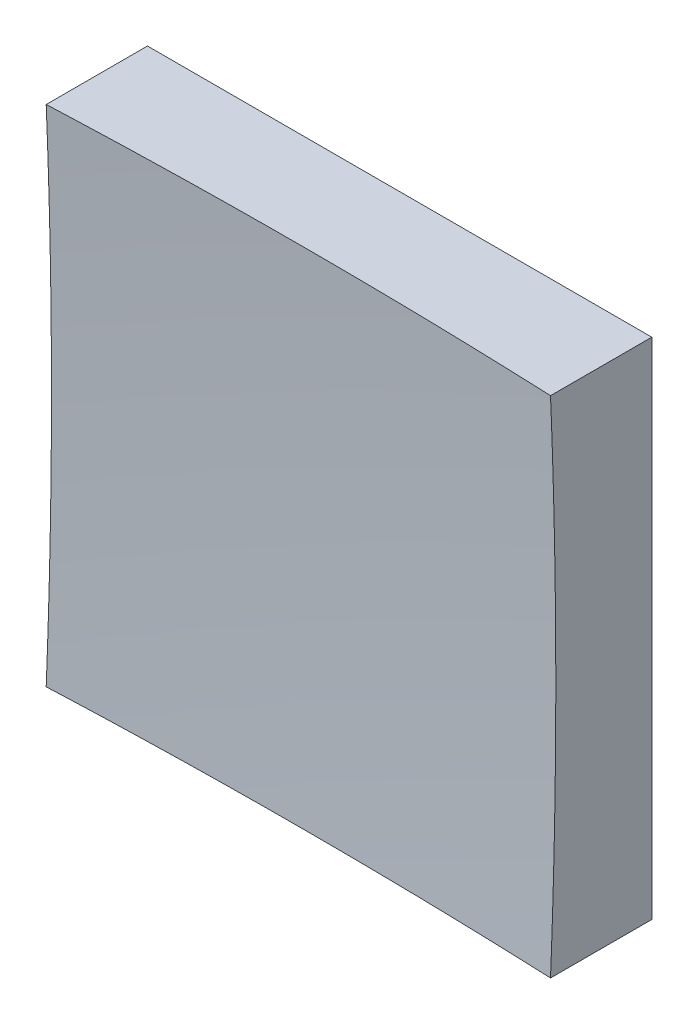
SolidWorks part; units mm, degrees
ref_plane "前视基准面" through (0, 0, 0) normal (0, 0, 1) x (1, 0, 0)
ref_plane "上视基准面" through (0, 0, 0) normal (0, 1, 0) x (1, 0, 0)
ref_plane "右视基准面" through (0, 0, 0) normal (1, 0, 0) x (0, 0, -1)
sketch "草图1" plane through (0, 0, 0) normal (0, 0, 1) x (1, 0, 0)
  line L1 (-25, 25) -> (25, 25)
  line L2 (-25, 25) -> (-25, -25)
  line L3 (-25, -25) -> (25, -25)
  line L4 (25, 25) -> (25, -25)
  line L5 (-25, 25) -> (25, -25) construction
  line L6 (-25, -25) -> (25, 25) construction
  point P0 (0, 0)
  dimension "D1" = 50
  dimension "D2" = 50
extrude "凸台-拉伸1" add sketch "草图1" along normal blind 50 contours L2 L3 L4 L1
sketch "草图2" plane through (0, 0, 0) normal (0, 1, 0) x (1, 0, 0)
  line L0 (-7.4603, -9) -> (7.3192, -9) construction
  line L1 (0, 0) -> (0, -12.1749) construction
  line L2 (584.9073, -475.2709) -> (0, -475.2709)
  line L3 (0, -475.2709) -> (0, -9)
  arc A1 (584.9073, -475.2709) -> (0, -9) centre (0, -609) ccw
  dimension "D2" = 1200
  dimension "D1" = 9
revolve "切除-旋转2" cut sketch "草图2" angle 360 about L3
